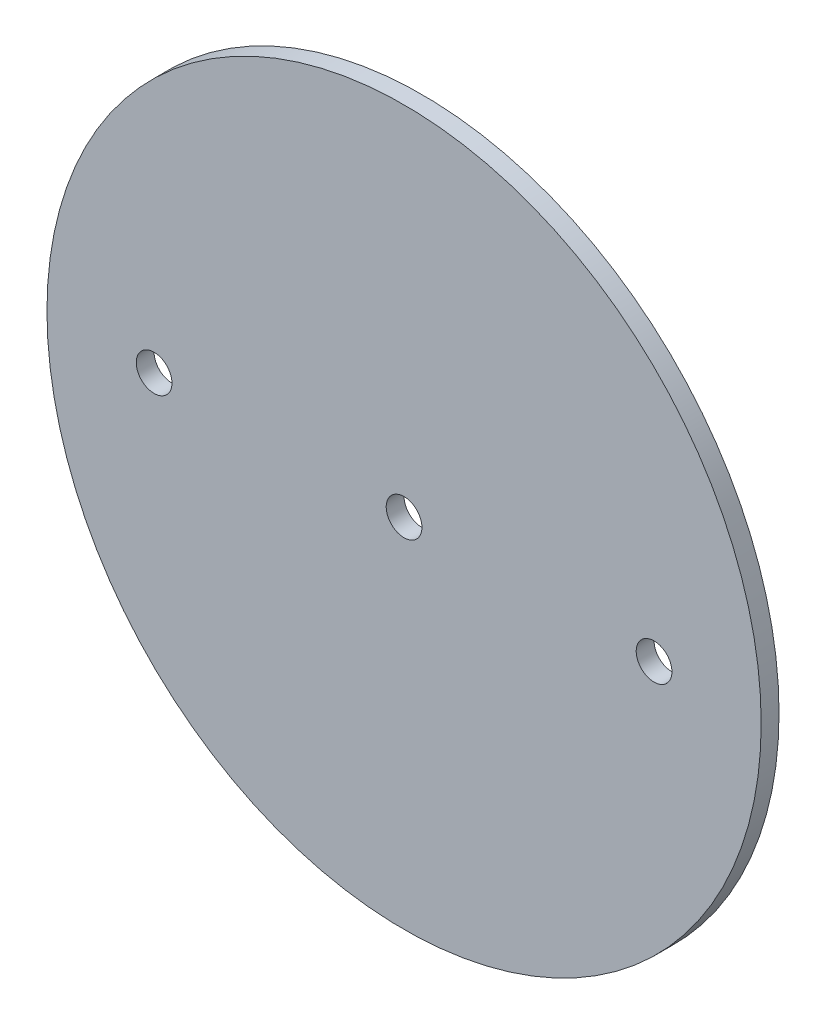
SolidWorks part; units mm, degrees
ref_plane "Front Plane" through (0, 0, 0) normal (0, 0, 1) x (1, 0, 0)
ref_plane "Top Plane" through (0, 0, 0) normal (0, 1, 0) x (1, 0, 0)
ref_plane "Right Plane" through (0, 0, 0) normal (1, 0, 0) x (0, 0, -1)
sketch "Sketch1" plane through (0, 0, 0) normal (0, 0, 1) x (1, 0, 0)
  circle A0 centre (0, 0) radius 63.5
  dimension "D1" = 127
extrude "Boss-Extrude1" add sketch "Sketch1" along normal mid plane 3.175
sketch "Sketch2" plane through (0, 0, 1.5875) normal (0, 0, 1) x (1, 0, 0)
  line L0 (-1000, 0) -> (49000, 0) construction
  point P1 (0, 0)
  point P4 (44.45, 0)
  point P5 (-44.45, 0)
  dimension "D1" = 44.45
  dimension "D2" = 88.9
hole_wizard "1/4 (0.25) Diameter Hole1" positions "Sketch2" profile "Sketch3" hole size "1/4" standard "ANSI Inch" end condition through all
sketch "Sketch3" plane through (-44.45, 0, 1.5875) normal (1, 0, 0) x (0, -1, 0)
  line L0 (0, 0) -> (0, 3.175)
  line L1 (0, 3.175) -> (3.175, 3.175)
  line L2 (3.175, 3.175) -> (3.175, 0)
  line L5 (3.175, 0) -> (0, 0)
  line L11 (0, -6.35) -> (0, 107.95) construction
  dimension "Thru Hole Dia." = 6.35
  dimension "Thru Hole Depth" = 3.175
equation "\"AIRFRAME_OD\"= 5.15in"
equation "\"AIRFRAME_ID\"= 5.00in"
equation "\"FLAT_T\"= 0.125in"
equation "\"NOSE_EXP_L\"= 27in"
equation "\"NOSE_SHOULDER_L\"= 5in"
equation "\"MAIN_L\"= 30in"
equation "\"RECO_COUP_L\"= 10in"
equation "\"RECO_SWITCH_L\"= 2in"
equation "\"DROGUE_L\"= 20in"
equation "\"ATS_FORE_COUP_L\"= 5.5in"
equation "\"ATS_AFT_COUP_L\"= 4.5in"
equation "\"LOWER_L\"= 30in"
equation "\"FIN_N\"= 4"
equation "\"CR_AFT_X\"= 0.5in"
equation "\"CR_FORE_X\"= 9.25in"
equation "\"FIN_ROOT\"= 8in"
equation "\"FIN_X\"= 0.75in"
equation "\"MOTOR_OD\"= 3.091in"
equation "\"MOTOR_ID\"= 3.00in"
equation "\"COUPLER_OD\"= 4.998in"
equation "\"COUPLER_ID\"= 4.88in"
equation "\"D1@Sketch1\"=\"AIRFRAME_ID\""
equation "\"D1@Boss-Extrude1\"=\"FLAT_T\""
equation "\"RECO_ROD_X\"= 3.5in"
equation "\"ATS_ROD_X\"= 3in"
equation "\"D1@Sketch2\"=\"RECO_ROD_X\"*0.5"
equation "\"D2@Sketch2\"=\"RECO_ROD_X\""
equation "\"MOTOR_L\"= 14in"
equation "\"MOTOR_LOWER_X\"= 2in"
